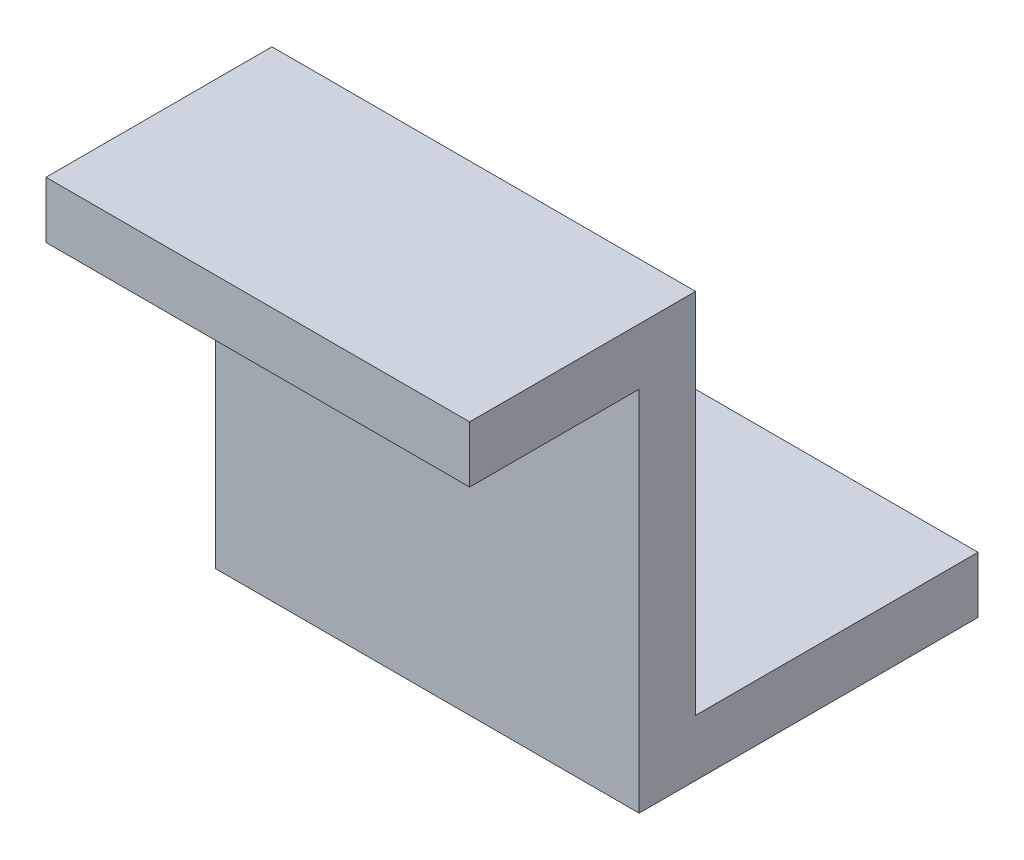
SolidWorks part; units mm, degrees
ref_plane "Front Plane" through (0, 0, 0) normal (0, 0, 1) x (1, 0, 0)
ref_plane "Top Plane" through (0, 0, 0) normal (0, 1, 0) x (1, 0, 0)
ref_plane "Right Plane" through (0, 0, 0) normal (1, 0, 0) x (0, 0, -1)
sketch "Sketch1" plane through (0, 0, 0) normal (1, 0, 0) x (0, 0, -1)
  line L0 (0, 0) -> (8, 0)
  line L1 (8, 0) -> (8, -13)
  line L2 (8, -13) -> (18, -13)
  line L3 (18, -13) -> (18, -15)
  line L4 (18, -15) -> (6, -15)
  line L5 (6, -15) -> (6, -2)
  line L6 (6, -2) -> (0, -2)
  line L7 (0, -2) -> (0, 0)
  dimension "D1" = 2
  dimension "D2" = 8
  dimension "D3" = 6
  dimension "D4" = 13
  dimension "D5" = 13
  dimension "D6" = 2
  dimension "D7" = 12
  dimension "D8" = 15
  dimension "D9" = 2
extrude "Boss-Extrude1" add sketch "Sketch1" against normal blind 15
sketch "Sketch3" plane through (0, -13, 0) normal (0, 1, 0) x (1, 0, 0)
  line L0 (-7.5, 18) -> (-7.5, 8) construction
  line L1 (-15, 18) -> (0, 18) construction
  line L2 (-15, 8) -> (0, 8) construction
  line L3 (0, 13) -> (-15, 13) construction
  line L4 (0, 18) -> (0, 8) construction
  line L5 (-15, 18) -> (-15, 8) construction
  circle A0 centre (-7.5, 13) radius 1.5
  dimension "D1" = 3
  dimension "D2" = 5
  dimension "D3" = 7.5
extrude "Cut-Extrude1" cut sketch "Sketch3" against normal up to next
